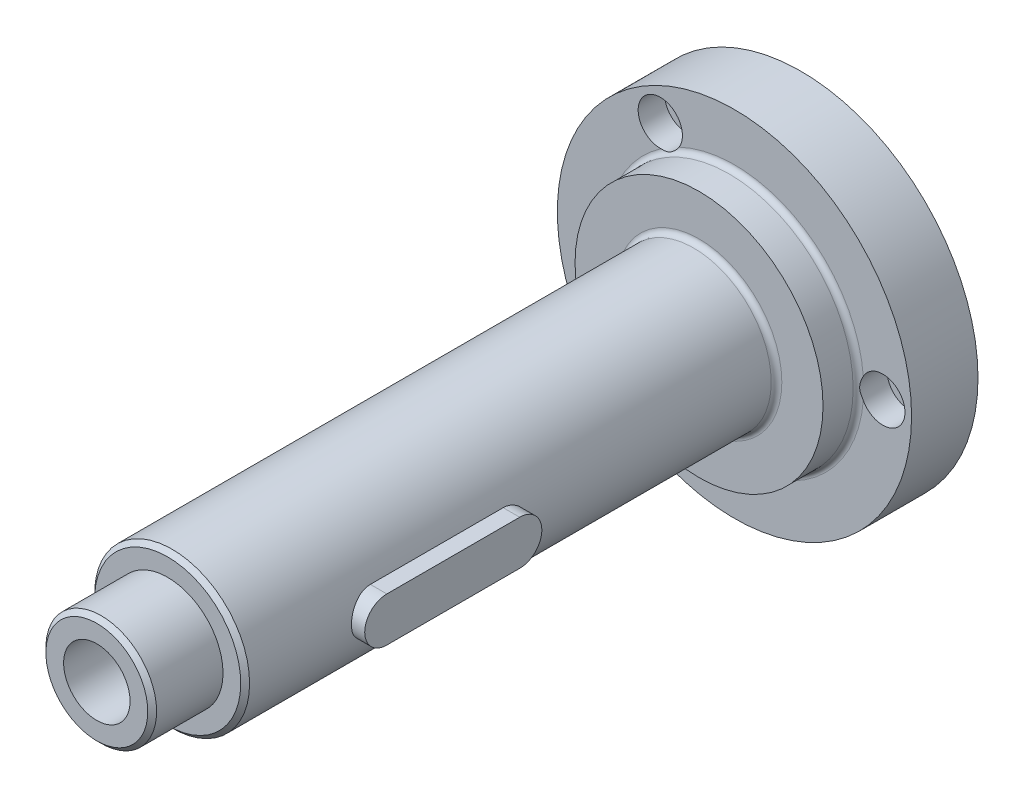
SolidWorks part; units mm, degrees
ref_plane "Alzado" through (0, 0, 0) normal (0, 0, 1) x (1, 0, 0)
ref_plane "Planta" through (0, 0, 0) normal (0, 1, 0) x (1, 0, 0)
ref_plane "Vista lateral" through (0, 0, 0) normal (1, 0, 0) x (0, 0, -1)
sketch "Croquis1" plane through (0, 0, 0) normal (0, 0, 1) x (1, 0, 0)
  circle A0 centre (0, 0) radius 28
  dimension "D1" = 56
extrude "Saliente-Extruir1" add sketch "Croquis1" along normal blind 3
sketch "Croquis2" plane through (0, 0, 3) normal (0, 0, 1) x (1, 0, 0)
  circle A0 centre (0, 0) radius 40
  dimension "D1" = 80
extrude "Saliente-Extruir2" add sketch "Croquis2" along normal blind 15
sketch "Croquis3" plane through (0, 0, 18) normal (0, 0, 1) x (1, 0, 0)
  circle A0 centre (0, 0) radius 28
  dimension "D1" = 56
extrude "Saliente-Extruir3" add sketch "Croquis3" along normal blind 8
sketch "Croquis4" plane through (0, 0, 26) normal (0, 0, 1) x (1, 0, 0)
  circle A0 centre (0, 0) radius 17.5
  dimension "D1" = 35
extrude "Saliente-Extruir4" add sketch "Croquis4" along normal blind 120
sketch "Croquis5" plane through (0, 0, 146) normal (0, 0, 1) x (1, 0, 0)
  circle A0 centre (0, 0) radius 12.5
  dimension "D1" = 25
extrude "Saliente-Extruir5" add sketch "Croquis5" along normal blind 16
fillet "Redondeo1" radius 1.2 2 edges at (17.5, 0, 26) (28, 0, 18)
chamfer "Chaflán1" distance 1 angle 45 2 edges at (12.5, 0, 162) (17.5, 0, 146)
sketch "Croquis6" plane through (0, 0, 0) normal (1, 0, 0) x (0, 0, -1)
  line L0 (-165.8933, 0) -> (0, 0) construction
  line L1 (-117, 0) -> (-87, 0) construction
  line L2 (-117, 5) -> (-87, 5)
  line L3 (-117, -5) -> (-87, -5)
  line L4 (-162, 11.5) -> (-162, -11.5) construction
  arc A0 (-117, 5) -> (-117, -5) centre (-117, 0) ccw
  arc A1 (-87, -5) -> (-87, 5) centre (-87, 0) ccw
  point P5 (-102, 0)
  dimension "D1" = 10
  dimension "D2" = 45
  dimension "D3" = 30
extrude "Cortar-Extruir1" cut sketch "Croquis6" along normal blind 33.2 from offset 12.5
sketch "Croquis7" plane through (0, 0, 0) normal (1, 0, 0) x (0, 0, -1)
  line L0 (-161, 0) -> (32.6264, 0) construction
  line L1 (-161, -12.5) -> (-161, 12.5) construction
  line L2 (-162, 0) -> (-162, 7.5)
  line L3 (-162, 11.5) -> (-162, -11.5) construction
  line L4 (-162, 7.5) -> (-52, 7.5)
  line L5 (-52, 7.5) -> (0, 8.89)
  line L6 (0, -28) -> (0, 28) construction
  line L7 (0, 8.89) -> (0, 0)
  line L8 (0, 0) -> (-162, 0)
  dimension "D1" = 15
  dimension "D2" = 110
  dimension "D3" = 17.78
  dimension "D4" = 1.531
revolve "Cortar-Revolución1" cut sketch "Croquis7" angle 360 about L0
sketch "Croquis8" plane through (0, 0, 3) normal (0, 0, -1) x (-1, 0, 0)
  line L0 (-33.5, 0) -> (0, 0) construction
  circle A0 centre (-33.5, 0) radius 3.25
  dimension "D2" = 6.5
  dimension "D1" = 33.5
extrude "Cortar-Extruir2" cut sketch "Croquis8" against normal blind 33.2
pattern_circular "MatrizC1" count 3 over 360 about axis through (0, 0, 0) along (0, 0, 1) of "Cortar-Extruir2"
sketch "Croquis9" plane through (0, 0, 18) normal (0, 0, 1) x (1, 0, 0)
  circle A0 centre (33.5, 0) radius 5
  dimension "D1" = 10
extrude "Cortar-Extruir3" cut sketch "Croquis9" against normal blind 6
pattern_circular "MatrizC2" count 3 over 360 about axis through (0, 0, 0) along (0, 0, 1) of "Cortar-Extruir3"
sketch "Croquis10" plane through (0, 0, 12) normal (0, 0, 1) x (1, 0, 0)
  circle A1 centre (33.5, 0) radius 5
  circle A2 centre (33.5, 0) radius 5
  dimension "D1" = 0
extrude "Cortar-Extruir4" cut sketch "Croquis10" along normal blind 23.5
pattern_circular "MatrizC3" count 3 over 360 about axis through (0, 0, 146) along (0, 0, -1) of "Cortar-Extruir4"
sketch "Croquis11" plane through (12.5, 0, 0) normal (1, 0, 0) x (0, 0, -1)
  line L2 (-117, -5) -> (-87, -5)
  line L3 (-87, 5) -> (-117, 5)
  line L4 (-117, -5) -> (-87, -5)
  line L5 (-87, 5) -> (-117, 5)
  arc A2 (-117, 5) -> (-117, -5) centre (-117, 0) ccw
  arc A3 (-87, -5) -> (-87, 5) centre (-87, 0) ccw
  arc A4 (-117, 5) -> (-117, -5) centre (-117, 0) ccw
  arc A5 (-87, -5) -> (-87, 5) centre (-87, 0) ccw
  dimension "D1" = 0
extrude "Saliente-Extruir6" add sketch "Croquis11" along normal blind 8 separate body
